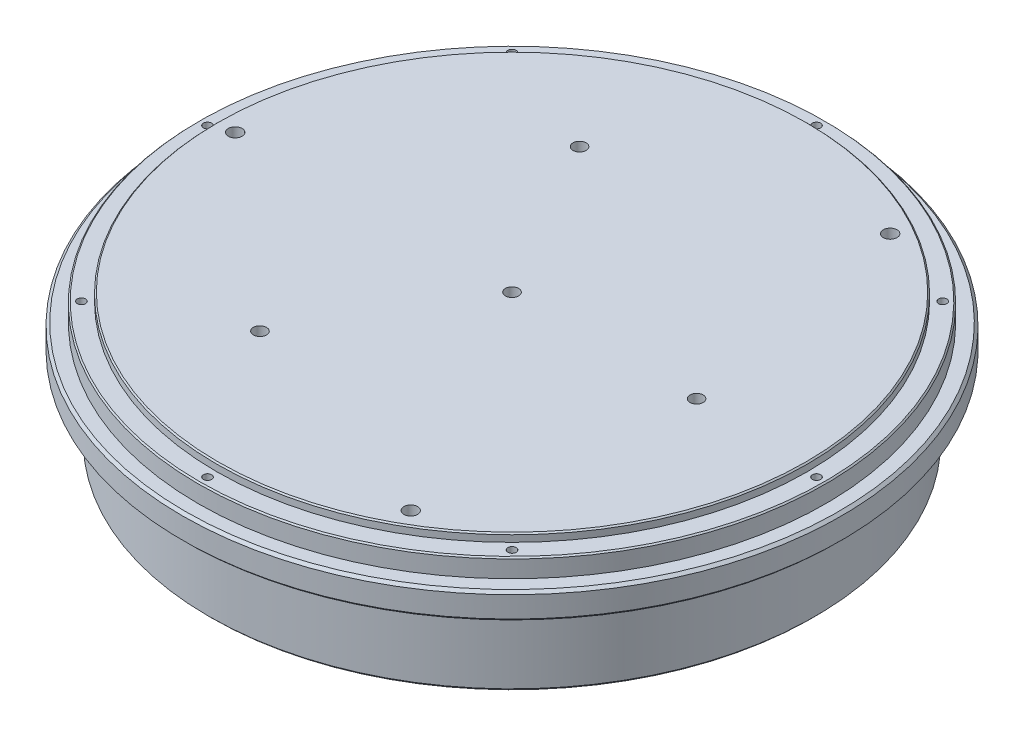
SolidWorks part; units mm, degrees
material "3.3315 (EN-AW 5005)"
ref_plane "Front Plane" through (0, 0, 0) normal (0, 0, 1) x (1, 0, 0)
ref_plane "Top Plane" through (0, 0, 0) normal (0, 1, 0) x (1, 0, 0)
ref_plane "Right Plane" through (0, 0, 0) normal (1, 0, 0) x (0, 0, -1)
sketch "Sketch1" plane through (0, 0, 0) normal (0, 1, 0) x (1, 0, 0)
  circle A0 centre (0, 0) radius 125
  dimension "D1" = 250
extrude "Boss-Extrude1" add sketch "Sketch1" along normal blind 50
sketch "Sketch2" plane through (0, 50, 0) normal (0, 1, 0) x (1, 0, 0)
  circle A0 centre (0, 0) radius 119
  circle A1 centre (0, 0) radius 127
  circle A2 centre (0, 0) radius 125 construction
  dimension "D1" = 254
  dimension "D2" = 6
extrude "Pakning" cut sketch "Sketch2" against normal blind 10
sketch "Sketch3" plane through (0, 50, 0) normal (0, 1, 0) x (1, 0, 0)
  circle A0 centre (0, 0) radius 112
  circle A1 centre (0, 0) radius 125
  circle A2 centre (0, 0) radius 125 construction
  circle A3 centre (0, 0) radius 119 construction
  dimension "D1" = 7
extrude "PakningsRing" cut sketch "Sketch3" against normal blind 3
sketch "Sketch5" plane through (0, 0, 0) normal (0, -1, 0) x (-1, 0, 0)
  line L0 (-42.4264, 42.4264) -> (0, 0) construction
  line L1 (-42.4264, 42.4264) -> (-84.1457, 84.1457) construction
  line L2 (0, 0) -> (0, 67.509) construction
  circle A0 centre (-42.4264, 42.4264) radius 5
  circle A2 centre (0, 0) radius 119 construction
  dimension "D1" = 10
  dimension "D2" = 60
  dimension "D3" = 45
extrude "Varmelement" [suppressed] cut sketch "Sketch5" against normal blind 45
pattern_circular "Varmeelement_pattern" [suppressed] count 4 over 360
sketch "Sketch7" plane through (0, 0, 0) normal (0, -1, 0) x (1, 0, 0)
  circle A0 centre (0, 0) radius 115
  circle A1 centre (0, 0) radius 135
  circle A2 centre (0, 0) radius 125 construction
  dimension "D1" = 10
  dimension "D2" = 230
extrude "Cut-Extrude6" cut sketch "Sketch7" against normal blind 30
chamfer "Chamfer2" distance 0.5 angle 45 2 edges at (0, 50, 112) (0, 47, 119)
hole_wizard "Tapped Hole for M3x0.5 Helicoil1" positions "Sketch16" profile "Sketch17" tap size "M3x0.5" standard "Helicoil® Metric"
sketch "Sketch16" plane through (0, 47, 0) normal (0, 1, 0) x (1, 0, 0)
  line L0 (0, 112) -> (0, 119) construction
  circle A0 centre (0, 0) radius 112 construction
  circle A2 centre (0, 0) radius 119 construction
  point P0 (0, 115.5)
sketch "Sketch17" plane through (0, 47, -115.5) normal (1, 0, 0) x (0, 0, 1)
  line L0 (0, 0) -> (0, 5.9464)
  line L1 (0, 5.9464) -> (1.575, 5)
  line L2 (1.575, 5) -> (1.575, 0)
  line L5 (1.575, 0) -> (0, 0)
  line L10 (0, 5.9464) -> (-1.575, 5) construction
  line L11 (0, -6.35) -> (0, 107.95) construction
  dimension "Tap Drill Dia." = 3.15
  dimension "Tap Drill Depth" = 5
  dimension "Drill Angle" = 118
cosmetic thread "Hole Thread2" parameters "D1"=3.5, "D2"=3.716
pattern_circular "CirPattern2" count 8 every 45 about axis through (0, 0, 0) along (0, 1, 0) of "Tapped Hole for M3x0.5 Helicoil1"
cosmetic thread "Hole Thread3" parameters "D1"=3.5, "D2"=3.716
cosmetic thread "Hole Thread4" parameters "D1"=3.5, "D2"=3.716
cosmetic thread "Hole Thread5" parameters "D1"=3.5, "D2"=3.716
cosmetic thread "Hole Thread6" parameters "D1"=3.5, "D2"=3.716
cosmetic thread "Hole Thread7" parameters "D1"=3.5, "D2"=3.716
cosmetic thread "Hole Thread8" parameters "D1"=3.5, "D2"=3.716
cosmetic thread "Hole Thread9" parameters "D1"=3.5, "D2"=3.716
sketch "Sketch19" plane through (0, 0, 0) normal (0, -1, 0) x (1, 0, 0)
  line L0 (-80, 0) -> (0, 0) construction
  circle A0 centre (-80, 0) radius 11
  dimension "D1" = 22
  dimension "D2" = 80
extrude "Spindle" cut sketch "Sketch19" against normal blind 15.5
pattern_circular "CirPattern4" count 3 over 360 about axis through (0, 0, 0) along (0, 1, 0) of "Spindle"
sketch "Sketch20" plane through (0, 0, 0) normal (0, -1, 0) x (-1, 0, 0)
  line L0 (0, 0) -> (35, -60.6218) construction
  line L1 (35, -60.6218) -> (-40, -69.282) construction
  line L2 (35, -60.6218) -> (80, 0) construction
  line L3 (35, -60.6218) -> (57.5, -99.5929) construction
  circle A0 centre (35, -60.6218) radius 5
  circle A3 centre (0, 0) radius 115 construction
  dimension "D1" = 10
  dimension "D2" = 70
sketch "Sketch23" plane through (0, 0, 0) normal (0, -1, 0) x (1, 0, 0)
  circle A0 centre (0, 0) radius 5
  circle A2 centre (-35, 60.6218) radius 5 construction
hole_wizard "Ø10.0 (10) Diameter Hole1" positions "Sketch26" profile "Sketch27" hole size "Ø10.0" standard "ISO"
sketch "Sketch26" plane through (0, 0, 0) normal (0, -1, 0) x (-1, 0, 0)
  point P0 (35, -60.6218)
sketch "Sketch27" plane through (-35, 0, 60.6218) normal (1, 0, 0) x (0, 0, -1)
  line L0 (0, 0) -> (0, 43.5043)
  line L1 (0, 43.5043) -> (5, 40.5)
  line L2 (5, 40.5) -> (5, 0)
  line L5 (5, 0) -> (0, 0)
  line L10 (0, 43.5043) -> (-5, 40.5) construction
  line L11 (0, -6.35) -> (0, 107.95) construction
  dimension "Hole Dia." = 10
  dimension "Hole Depth" = 40.5
  dimension "Drill Angle" = 118
hole_wizard "Ø10.0 (10) Diameter Hole2" positions "Sketch28" profile "Sketch29" hole size "Ø10.0" standard "ISO"
sketch "Sketch28" plane through (0, 0, 0) normal (0, -1, 0) x (-1, 0, 0)
  point P0 (0, 0)
sketch "Sketch29" plane through (0, 0, 0) normal (1, 0, 0) x (0, 0, -1)
  line L0 (0, 0) -> (0, 43.5043)
  line L1 (0, 43.5043) -> (5, 40.5)
  line L2 (5, 40.5) -> (5, 0)
  line L5 (5, 0) -> (0, 0)
  line L10 (0, 43.5043) -> (-5, 40.5) construction
  line L11 (0, -6.35) -> (0, 107.95) construction
  dimension "Hole Dia." = 10
  dimension "Hole Depth" = 40.5
  dimension "Drill Angle" = 118
hole_wizard "Ø5.0 (5) Diameter Hole1" positions "Sketch30" profile "Sketch31" hole size "Ø5.0" standard "ISO"
sketch "Sketch30" plane through (0, 50, 0) normal (0, 1, 0) x (1, 0, 0)
  circle A0 centre (-35, -60.6218) radius 5 construction
  point P0 (-35, -60.6218)
sketch "Sketch31" plane through (-35, 50, 60.6218) normal (1, 0, 0) x (0, 0, 1)
  line L0 (0, 0) -> (0, 11.5022)
  line L1 (0, 11.5022) -> (2.5, 10)
  line L2 (2.5, 10) -> (2.5, 0)
  line L5 (2.5, 0) -> (0, 0)
  line L10 (0, 11.5022) -> (-2.5, 10) construction
  line L11 (0, -6.35) -> (0, 107.95) construction
  dimension "Hole Dia." = 5
  dimension "Hole Depth" = 10
  dimension "Drill Angle" = 118
hole_wizard "Ø5.0 (5) Diameter Hole2" positions "Sketch32" profile "Sketch33" hole size "Ø5.0" standard "ISO"
sketch "Sketch32" plane through (0, 50, 0) normal (0, 1, 0) x (1, 0, 0)
  point P0 (0, 0)
sketch "Sketch33" plane through (0, 50, 0) normal (1, 0, 0) x (0, 0, 1)
  line L0 (0, 0) -> (0, 11.5022)
  line L1 (0, 11.5022) -> (2.5, 10)
  line L2 (2.5, 10) -> (2.5, 0)
  line L5 (2.5, 0) -> (0, 0)
  line L10 (0, 11.5022) -> (-2.5, 10) construction
  line L11 (0, -6.35) -> (0, 107.95) construction
  dimension "Hole Dia." = 5
  dimension "Hole Depth" = 10
  dimension "Drill Angle" = 118
hole_wizard "Ø5.0 (5) Diameter Hole3" positions "Sketch34" profile "Sketch35" hole size "Ø5.0" standard "ISO"
sketch "Sketch34" plane through (0, 0, 0) normal (0, -1, 0) x (-1, 0, 0)
  line L0 (35, -60.6218) -> (-20, -34.641) construction
  line L1 (-20, -34.641) -> (-70, 0) construction
  line L3 (0, 0) -> (-20, -34.641) construction
  line L4 (-20, -34.641) -> (-40, -69.282) construction
  point P0 (-20, -34.641)
  dimension "D1" = 40
sketch "Sketch35" plane through (20, 0, 34.641) normal (1, 0, 0) x (0, 0, -1)
  line L0 (0, 0) -> (0, 22.0022)
  line L1 (0, 22.0022) -> (2.5, 20.5)
  line L2 (2.5, 20.5) -> (2.5, 0)
  line L5 (2.5, 0) -> (0, 0)
  line L10 (0, 22.0022) -> (-2.5, 20.5) construction
  line L11 (0, -6.35) -> (0, 107.95) construction
  dimension "Hole Dia." = 5
  dimension "Hole Depth" = 20.5
  dimension "Drill Angle" = 118
hole_wizard "M4 Tapped Hole1" positions "Sketch36" profile "Sketch37" tap size "M4" standard "ISO"
sketch "Sketch36" plane through (0, 0, 0) normal (0, -1, 0) x (-1, 0, 0)
  line L0 (43.2272, -55.8718) -> (26.7728, -65.3718) construction
  line L2 (35, -60.6218) -> (0, 0) construction
  circle A0 centre (35, -60.6218) radius 5 construction
  point P0 (43.2272, -55.8718)
  point P2 (26.7728, -65.3718)
  point P8 (35, -60.6218)
  dimension "D1" = 19
sketch "Sketch37" plane through (-43.2272, 0, 55.8718) normal (1, 0, 0) x (0, 0, -1)
  line L0 (0, 0) -> (0, 11.0914)
  line L1 (0, 11.0914) -> (1.65, 10.1)
  line L2 (1.65, 10.1) -> (1.65, 0)
  line L5 (1.65, 0) -> (0, 0)
  line L10 (0, 11.0914) -> (-1.65, 10.1) construction
  line L11 (0, -6.35) -> (0, 107.95) construction
  dimension "Tap Drill Dia." = 3.3
  dimension "Tap Drill Depth" = 10.1
  dimension "Drill Angle" = 118
cosmetic thread "Hole Thread10" parameters "D1"=8, "D2"=4
cosmetic thread "Hole Thread11" parameters "D1"=8, "D2"=4
hole_wizard "M4 Tapped Hole2" positions "Sketch38" profile "Sketch39" tap size "M4" standard "ISO"
sketch "Sketch38" plane through (0, 0, 0) normal (0, -1, 0) x (-1, 0, 0)
  line L0 (8.2272, -4.75) -> (0, 0) construction
  line L1 (0, 0) -> (-8.2272, 4.75) construction
  line L3 (26.7728, 65.3718) -> (43.2272, 55.8718) construction
  point P0 (8.2272, -4.75)
  point P2 (-8.2272, 4.75)
  dimension "D1" = 19
sketch "Sketch39" plane through (-8.2272, 0, 4.75) normal (1, 0, 0) x (0, 0, -1)
  line L0 (0, 0) -> (0, 11.0914)
  line L1 (0, 11.0914) -> (1.65, 10.1)
  line L2 (1.65, 10.1) -> (1.65, 0)
  line L5 (1.65, 0) -> (0, 0)
  line L10 (0, 11.0914) -> (-1.65, 10.1) construction
  line L11 (0, -6.35) -> (0, 107.95) construction
  dimension "Tap Drill Dia." = 3.3
  dimension "Tap Drill Depth" = 10.1
  dimension "Drill Angle" = 118
cosmetic thread "Hole Thread16" parameters "D1"=8, "D2"=4
cosmetic thread "Hole Thread17" parameters "D1"=8, "D2"=4
hole_wizard "M4 Tapped Hole3" positions "Sketch40" profile "Sketch41" tap size "M4" standard "ISO"
sketch "Sketch40" plane through (0, 0, 0) normal (0, -1, 0) x (-1, 0, 0)
  line L0 (-13.5048, -38.391) -> (-20, -34.641) construction
  line L1 (-20, -34.641) -> (-26.4952, -30.891) construction
  line L3 (0, 0) -> (-20, -34.641) construction
  point P0 (-13.5048, -38.391)
  point P2 (-26.4952, -30.891)
  dimension "D1" = 15
sketch "Sketch41" plane through (13.5048, 0, 38.391) normal (1, 0, 0) x (0, 0, -1)
  line L0 (0, 0) -> (0, 11.0914)
  line L1 (0, 11.0914) -> (1.65, 10.1)
  line L2 (1.65, 10.1) -> (1.65, 0)
  line L5 (1.65, 0) -> (0, 0)
  line L10 (0, 11.0914) -> (-1.65, 10.1) construction
  line L11 (0, -6.35) -> (0, 107.95) construction
  dimension "Tap Drill Dia." = 3.3
  dimension "Tap Drill Depth" = 10.1
  dimension "Drill Angle" = 118
cosmetic thread "Hole Thread18" parameters "D1"=8, "D2"=4
cosmetic thread "Hole Thread19" parameters "D1"=8, "D2"=4
sketch "Sketch18" plane through (0, 47, 0) normal (0, 1, 0) x (1, 0, 0)
  line L0 (70, 0) -> (0, 0) construction
  line L1 (0, 0) -> (-35, 60.6218) construction
  line L2 (52.5, 90.9327) -> (0, 0) construction
  line L3 (-35, 60.6218) -> (52.5, 90.9327) construction
  line L4 (52.5, 90.9327) -> (70, 0) construction
  circle A0 centre (52.5, 90.9327) radius 2.5
  circle A1 centre (0, 0) radius 105 construction
  dimension "D2" = 210
hole_wizard "Tapped Hole for M5x0.8 Helicoil1" positions "Sketch42" profile "Sketch43" tap size "M5x0.8" standard "Helicoil® Metric"
sketch "Sketch42" plane through (0, 50, 0) normal (0, 1, 0) x (1, 0, 0)
  point P0 (52.5, 90.9327)
sketch "Sketch43" plane through (52.5, 50, -90.9327) normal (1, 0, 0) x (0, 0, 1)
  line L0 (0, 0) -> (0, 9.7622)
  line L1 (0, 9.7622) -> (2.6, 8.2)
  line L2 (2.6, 8.2) -> (2.6, 0)
  line L5 (2.6, 0) -> (0, 0)
  line L10 (0, 9.7622) -> (-2.6, 8.2) construction
  line L11 (0, -6.35) -> (0, 107.95) construction
  dimension "Tap Drill Dia." = 5.2
  dimension "Tap Drill Depth" = 8.2
  dimension "Drill Angle" = 118
cosmetic thread "Hole Thread20" parameters "D1"=5.8, "D2"=6.145
pattern_circular "CirPattern8" count 3 over 360 about axis through (0, 0, 0) along (0, 1, 0) of "Tapped Hole for M5x0.8 Helicoil1"
cosmetic thread "Hole Thread21" parameters "D1"=5.8, "D2"=6.145
cosmetic thread "Hole Thread22" parameters "D1"=5.8, "D2"=6.145
pattern_circular "CirPattern9" count 3 over 360 about axis through (0, 0, 0) along (0, 1, 0) of "Ø10.0 (10) Diameter Hole1", "M4 Tapped Hole1", "Ø5.0 (5) Diameter Hole1"
cosmetic thread "Hole Thread23" parameters "D1"=8, "D2"=4
cosmetic thread "Hole Thread24" parameters "D1"=8, "D2"=4
cosmetic thread "Hole Thread25" parameters "D1"=8, "D2"=4
cosmetic thread "Hole Thread26" parameters "D1"=8, "D2"=4
chamfer "Chamfer3" distance 1 angle 45 3 edges at (0, 0, -115) (0, 30, -125) (0, 40, 125)
